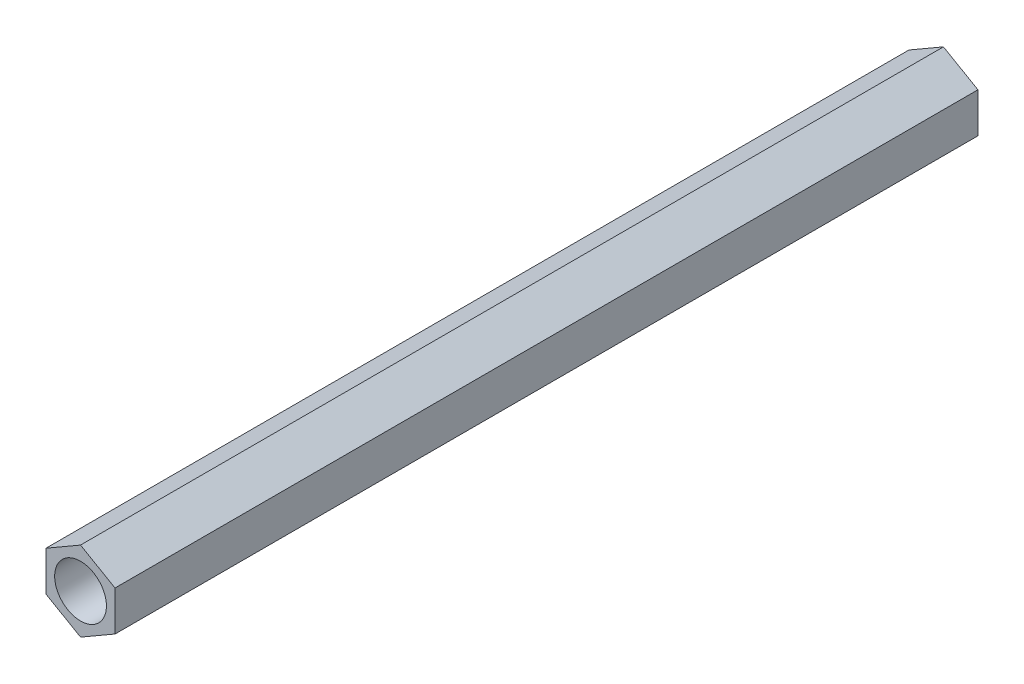
SolidWorks part; units mm, degrees
ref_plane "Plan de face" through (0, 0, 0) normal (0, 0, 1) x (1, 0, 0)
ref_plane "Plan de dessus" through (0, 0, 0) normal (0, 1, 0) x (1, 0, 0)
ref_plane "Plan de droite" through (0, 0, 0) normal (1, 0, 0) x (0, 0, -1)
sketch "Esquisse1" plane through (0, 0, 0) normal (0, 0, 1) x (1, 0, 0)
  line L1 (2.0012, -1.1526) -> (1.9988, 1.1568)
  line L2 (1.9988, 1.1568) -> (-0.0024, 2.3094)
  line L3 (-0.0024, 2.3094) -> (-2.0012, 1.1526)
  line L4 (-2.0012, 1.1526) -> (-1.9988, -1.1568)
  line L5 (-1.9988, -1.1568) -> (0.0024, -2.3094)
  line L6 (0.0024, -2.3094) -> (2.0012, -1.1526)
  circle A0 centre (0, 0) radius 1.5
  circle A1 centre (0, 0) radius 2 construction
extrude "Boss.-Extru.1" add sketch "Esquisse1" along normal blind 50
